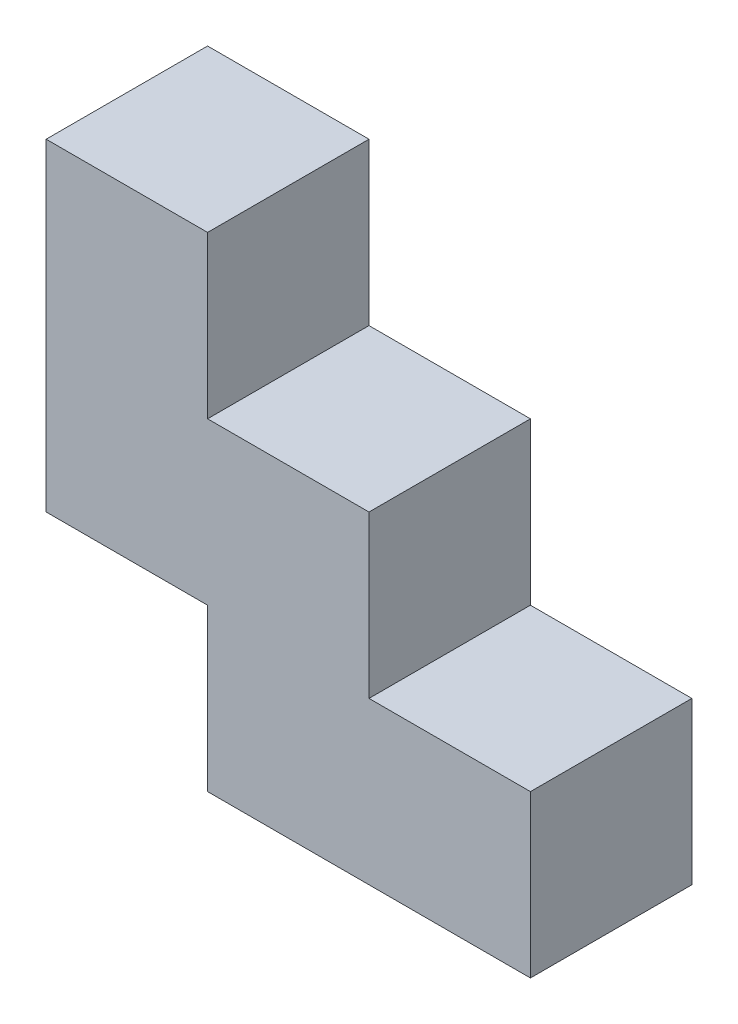
SolidWorks part; units mm, degrees
ref_plane "Front Plane" through (0, 0, 0) normal (0, 0, 1) x (1, 0, 0)
ref_plane "Top Plane" through (0, 0, 0) normal (0, 1, 0) x (1, 0, 0)
ref_plane "Right Plane" through (0, 0, 0) normal (1, 0, 0) x (0, 0, -1)
sketch "Sketch1" plane through (0, 0, 0) normal (0, 0, 1) x (1, 0, 0)
  line L66 (76.2, 0) -> (76.2, 25.4)
  line L67 (76.2, 25.4) -> (50.8, 25.4)
  line L68 (50.8, 25.4) -> (50.8, 50.8)
  line L69 (50.8, 50.8) -> (25.4, 50.8)
  line L70 (25.4, 50.8) -> (25.4, 76.2)
  line L71 (25.4, 76.2) -> (0, 76.2)
  line L72 (0, 76.2) -> (0, 25.4)
  line L73 (0, 25.4) -> (25.4, 25.4)
  line L74 (25.4, 25.4) -> (25.4, 0)
  line L75 (25.4, 0) -> (50.8, 0)
  line L76 (50.8, 0) -> (76.2, 0)
extrude "Boss-Extrude1" add sketch "Sketch1" along normal blind 25.4
